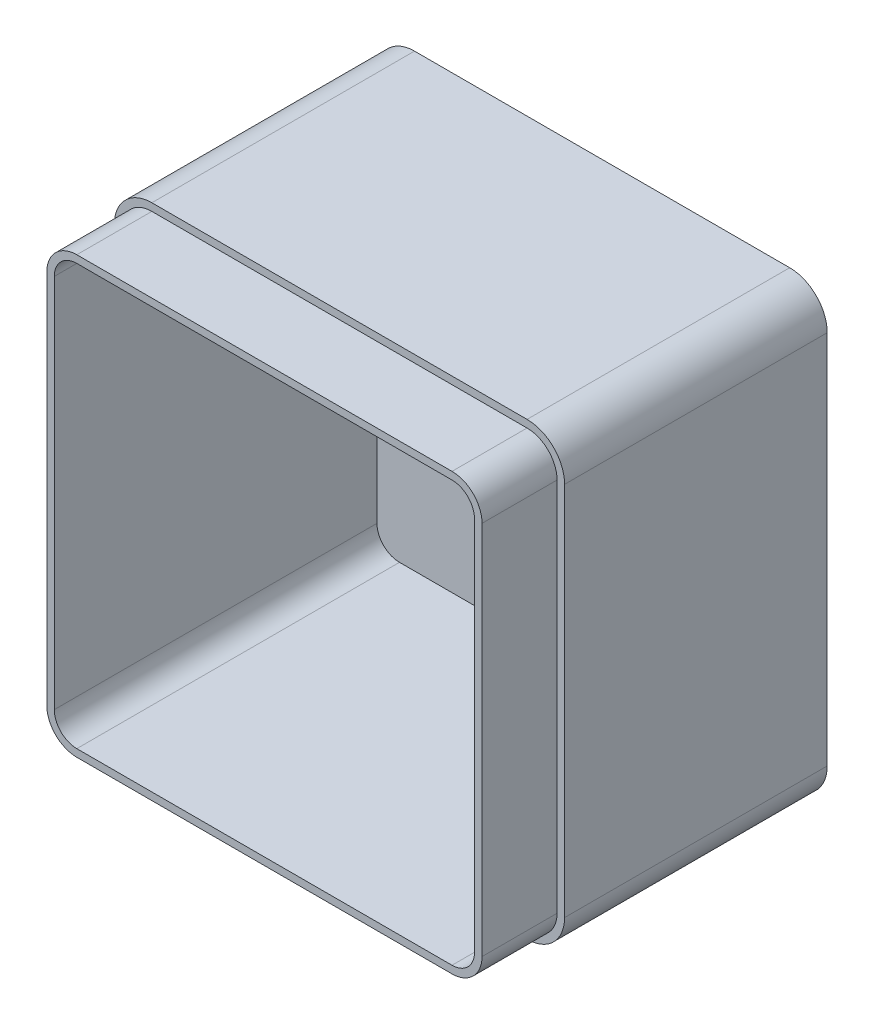
SolidWorks part; units mm, degrees
ref_plane "Front Plane" through (0, 0, 0) normal (0, 0, 1) x (1, 0, 0)
ref_plane "Top Plane" through (0, 0, 0) normal (0, 1, 0) x (1, 0, 0)
ref_plane "Right Plane" through (0, 0, 0) normal (1, 0, 0) x (0, 0, -1)
sketch "Sketch1" plane through (0, 0, 0) normal (0, 0, 1) x (1, 0, 0)
  line L1 (0, 0) -> (120, 0)
  line L2 (0, 0) -> (0, 120)
  line L3 (0, 120) -> (120, 120)
  line L4 (120, 0) -> (120, 120)
  dimension "D1" = 120
  dimension "D2" = 120
extrude "Boss-Extrude1" add sketch "Sketch1" along normal blind 90
fillet "Fillet1" radius 10 4 edges at (120, 0, 45) (0, 0, 45) (0, 120, 45) (120, 120, 45)
shell "Shell1" thickness 4
sketch "Sketch2" plane through (0, 0, 90) normal (0, 0, 1) x (1, 0, 0)
  line L0 (10, 2) -> (110, 2)
  line L1 (118, 10) -> (118, 110)
  line L2 (110, 118) -> (10, 118)
  line L3 (2, 110) -> (2, 10)
  line L4 (10, 0) -> (110, 0)
  line L5 (120, 10) -> (120, 110)
  line L6 (110, 120) -> (10, 120)
  line L7 (0, 110) -> (0, 10)
  line L8 (10, 0) -> (110, 0)
  line L9 (120, 10) -> (120, 110)
  line L10 (110, 120) -> (10, 120)
  line L11 (0, 110) -> (0, 10)
  arc A0 (110, 2) -> (118, 10) centre (110, 10) ccw
  arc A1 (118, 110) -> (110, 118) centre (110, 110) ccw
  arc A2 (10, 118) -> (2, 110) centre (10, 110) ccw
  arc A3 (2, 10) -> (10, 2) centre (10, 10) ccw
  arc A4 (110, 0) -> (120, 10) centre (110, 10) ccw
  arc A5 (120, 110) -> (110, 120) centre (110, 110) ccw
  arc A6 (10, 120) -> (0, 110) centre (10, 110) ccw
  arc A7 (0, 10) -> (10, 0) centre (10, 10) ccw
  arc A8 (110, 0) -> (120, 10) centre (110, 10) ccw
  arc A9 (120, 110) -> (110, 120) centre (110, 110) ccw
  arc A10 (10, 120) -> (0, 110) centre (10, 110) ccw
  arc A11 (0, 10) -> (10, 0) centre (10, 10) ccw
  dimension "D1" = 0
  dimension "D2" = 2
extrude "Cut-Extrude1" cut sketch "Sketch2" against normal blind 20
